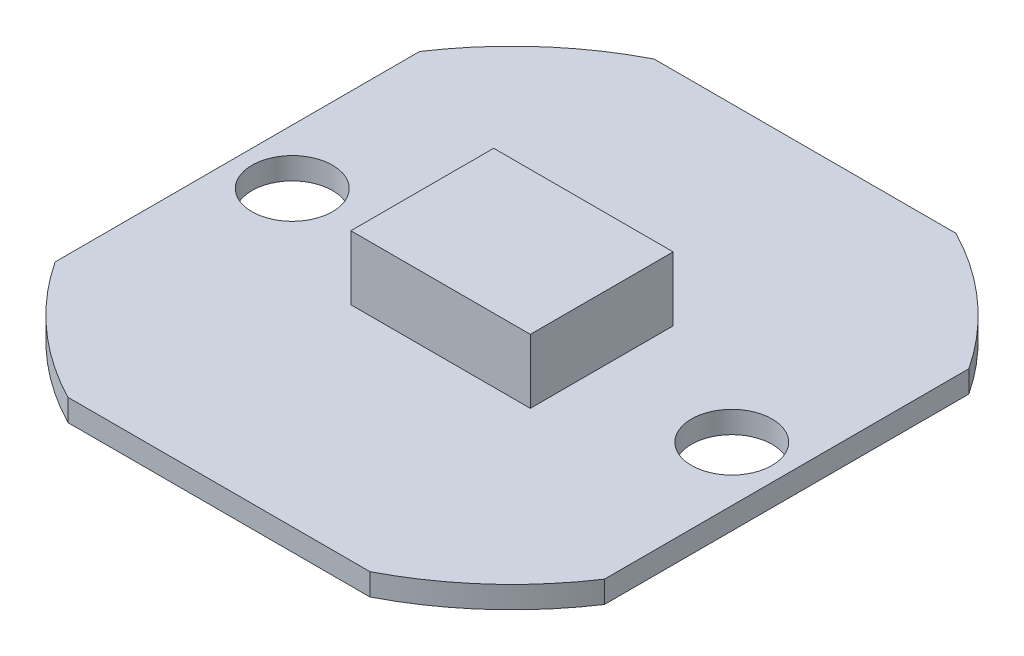
SolidWorks part; units mm, degrees
ref_plane "前视基准面" through (0, 0, 0) normal (0, 0, 1) x (1, 0, 0)
ref_plane "上视基准面" through (0, 0, 0) normal (0, 1, 0) x (1, 0, 0)
ref_plane "右视基准面" through (0, 0, 0) normal (1, 0, 0) x (0, 0, -1)
sketch "草图1" plane through (0, 0, 0) normal (0, 1, 0) x (1, 0, 0)
  line L1 (-4.1231, 8) -> (4.1231, 8)
  line L3 (-7.5, -4.9749) -> (-7.5, 4.9749)
  line L4 (7.5, -4.9749) -> (7.5, 4.9749)
  line L5 (-4.1231, -8) -> (4.1231, -8)
  arc A1 (-7.5, 4.9749) -> (-4.1231, 8) centre (0, 0) cw
  arc A2 (7.5, 4.9749) -> (4.1231, 8) centre (0, 0) ccw
  arc A3 (7.5, -4.9749) -> (4.1231, -8) centre (0, 0) cw
  arc A4 (-7.5, -4.9749) -> (-4.1231, -8) centre (0, 0) ccw
  circle A5 centre (-6, 0) radius 1.1
  circle A6 centre (6, 0) radius 1.1
extrude "凸台-拉伸1" add sketch "草图1" along normal blind 0.6
sketch "草图2" plane through (0, 0.6, 0) normal (0, 1, 0) x (1, 0, 0)
  line L1 (2.45, 1.95) -> (-2.45, 1.95)
  line L2 (-2.45, 1.95) -> (-2.45, -1.95)
  line L3 (-2.45, -1.95) -> (2.45, -1.95)
  line L5 (2.45, 1.95) -> (2.45, -1.95)
  point P7 (0, -1.95)
extrude "凸台-拉伸2" add sketch "草图2" along normal blind 1.75
